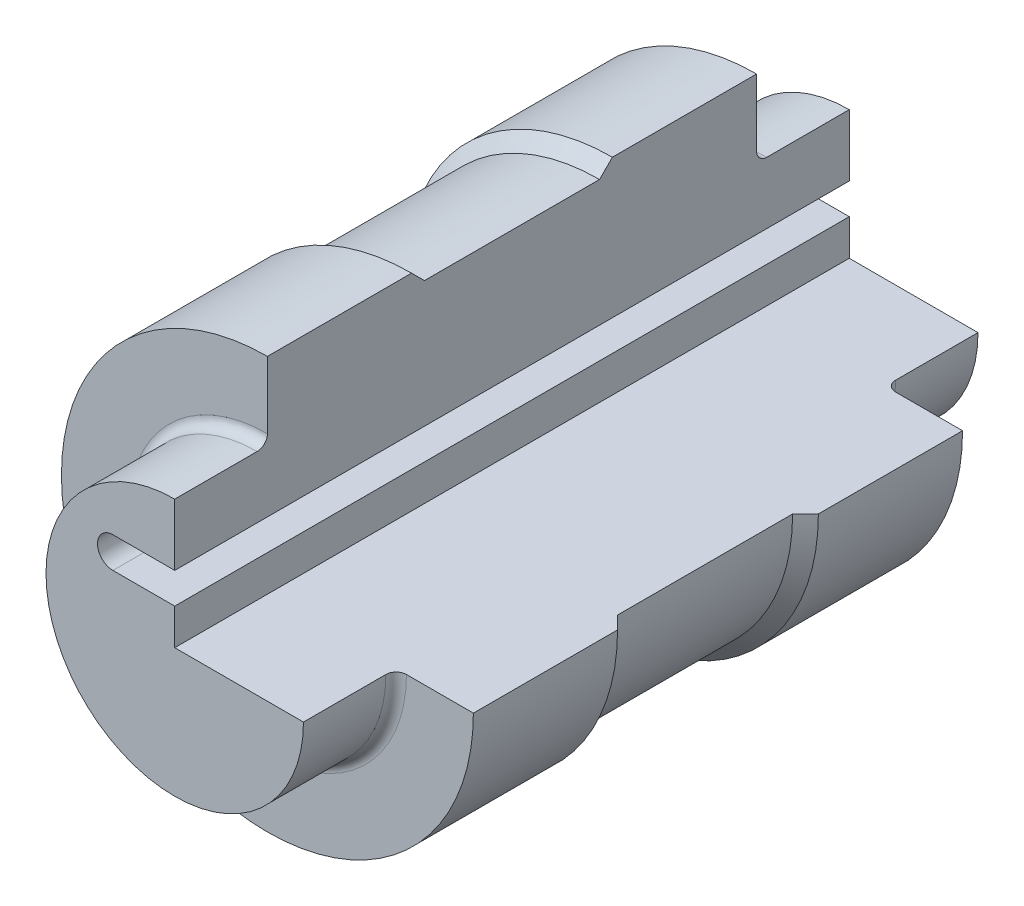
SolidWorks part; units mm, degrees
material "AISI 1020"
ref_plane "Front Plane" through (0, 0, 0) normal (0, 0, 1) x (1, 0, 0)
ref_plane "Top Plane" through (0, 0, 0) normal (0, 1, 0) x (1, 0, 0)
ref_plane "Right Plane" through (0, 0, 0) normal (1, 0, 0) x (0, 0, -1)
sketch "Sketch1" plane through (0, 0, 0) normal (1, 0, 0) x (0, 0, -1)
  line L0 (0, 33.8319) -> (0, -14.886) construction
  line L1 (65.5, 0) -> (-65.5, 0)
  line L2 (-65.5, 0) -> (-65.5, 25)
  line L3 (-65.5, 25) -> (-49.5, 25)
  line L4 (-47.5, 40) -> (-47.5, 27)
  line L5 (-47.5, 40) -> (-19.5, 40)
  line L6 (-19.5, 40) -> (-17, 37.5)
  line L7 (-17, 37.5) -> (17, 37.5)
  line L8 (65.5, 0) -> (65.5, 25)
  line L9 (65.5, 25) -> (49.5, 25)
  line L10 (47.5, 40) -> (47.5, 27)
  line L11 (47.5, 40) -> (19.5, 40)
  line L12 (19.5, 40) -> (17, 37.5)
  arc A0 (-49.5, 25) -> (-47.5, 27) centre (-49.5, 27) ccw
  arc A1 (49.5, 25) -> (47.5, 27) centre (49.5, 27) cw
  point P12 (0, 0)
  point P17 (0, 37.5)
  point P19 (-47.5, 25)
  point P22 (47.5, 25)
  dimension "D3" = 2
  dimension "D4" = 2
  dimension "D1" = 25
  dimension "D2" = 40
  dimension "D5" = 18
  dimension "D6" = 28
  dimension "D7" = 2.5
  dimension "D8" = 45
  dimension "D9" = 131
revolve "Revolve1" add sketch "Sketch1" angle 360 about L1
sketch "Sketch2" plane through (0, 0, 0) normal (0, 0, 1) x (1, 0, 0)
  line L0 (0, 40) -> (0, 13)
  line L1 (0, 0) -> (40, 0)
  line L2 (-12, 10) -> (3.2622, 10) construction
  line L3 (-12, 13) -> (0, 13)
  line L4 (-12, 7) -> (0, 7)
  line L5 (0, 7) -> (0, 0)
  circle A1 centre (0, 0) radius 40 construction
  arc A2 (-12, 13) -> (-12, 7) centre (-12, 10) ccw
  arc A4 (0, 40) -> (40, 0) centre (0, 0) cw
  point P8 (-4.3689, 10)
  dimension "D2" = 3
  dimension "D1" = 7
  dimension "D3" = 12
extrude "Cut-Extrude1" cut sketch "Sketch2" against normal through all both and the other way through all
equation "\"A\"= 131"
equation "\"B\"= 18"
equation "\"C\"= 28"
equation "\"D5@Sketch1\"=\"B\""
equation "\"D6@Sketch1\"=\"C\""
equation "\"D9@Sketch1\"=\"A\""
